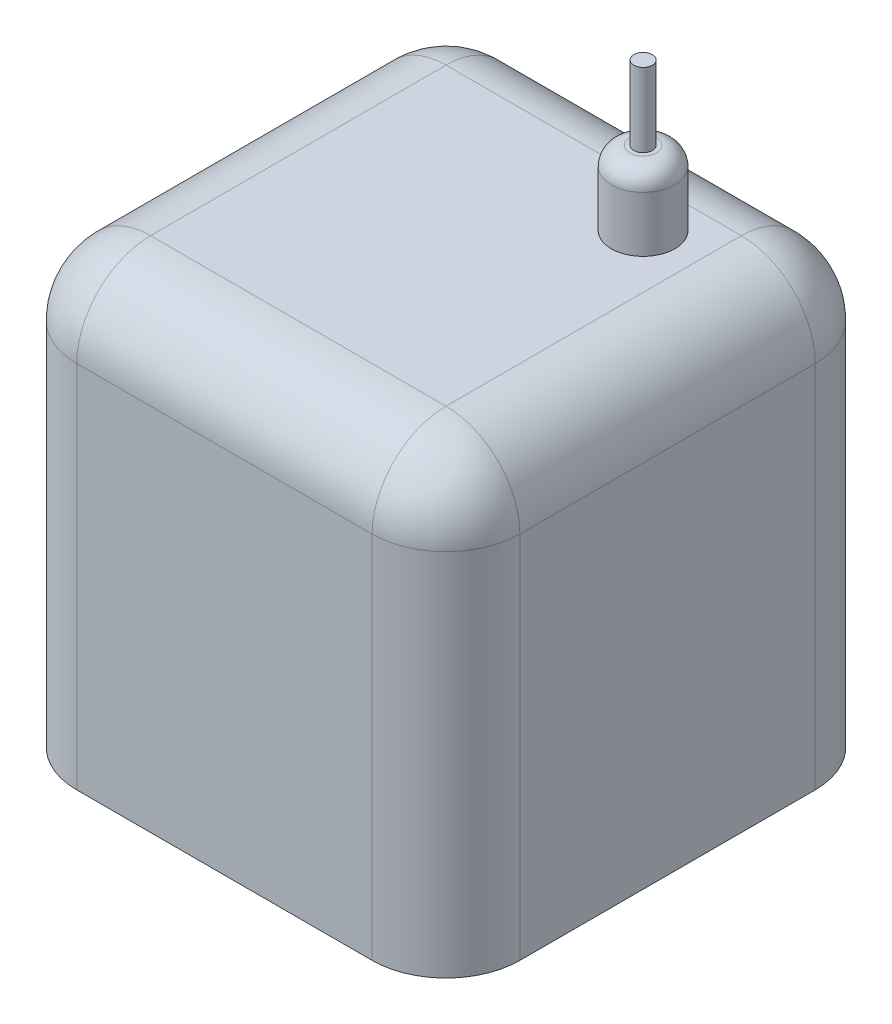
SolidWorks part; units mm, degrees
ref_plane "Front Plane" through (0, 0, 0) normal (0, 0, 1) x (1, 0, 0)
ref_plane "Top Plane" through (0, 0, 0) normal (0, 1, 0) x (1, 0, 0)
ref_plane "Right Plane" through (0, 0, 0) normal (1, 0, 0) x (0, 0, -1)
sketch "Sketch1" plane through (0, 0, 0) normal (0, 1, 0) x (1, 0, 0)
  line L0 (155.1457, -147.4298) -> (114, -106.284) construction
  line L7 (-6, 13.716) -> (114, 13.716)
  line L8 (-6, 13.716) -> (-6, -106.284)
  line L9 (-6, -106.284) -> (114, -106.284)
  line L10 (114, 13.716) -> (114, -106.284)
  line L11 (-6, 13.716) -> (152.567, -144.851) construction
  line L12 (-6, -106.284) -> (146.9038, -153.0929) construction
  point P0 (0, 0)
  point P6 (166.9438, -159.2278)
  dimension "D1" = 120
  dimension "D2" = 120
  dimension "D3" = 10
  dimension "D4" = 10
extrude "Boss-Extrude1" add sketch "Sketch1" along normal blind 120
fillet "Fillet1" radius 20 8 edges at (54, 120, 106.284) (-6, 120, 46.284) (54, 120, -13.716) (114, 120, 46.284) (-6, 60, -13.716) (114, 60, 106.284) (114, 60, -13.716) (-6, 60, 106.284)
sketch "Sketch4" plane through (0, 120, 0) normal (0, 1, 0) x (1, 0, 0)
  circle A0 centre (79.4733, -18.3747) radius 8.6065
extrude "Boss-Extrude4" add sketch "Sketch4" along normal blind 20
sketch "Sketch5" plane through (0, 140, 0) normal (0, 1, 0) x (1, 0, 0)
  circle A0 centre (79.4733, -18.3747) radius 2.5
  dimension "D1" = 5
extrude "Boss-Extrude5" add sketch "Sketch5" along normal blind 20
fillet "Fillet2" radius 5 1 edges at (79.4733, 140, 26.9812)
